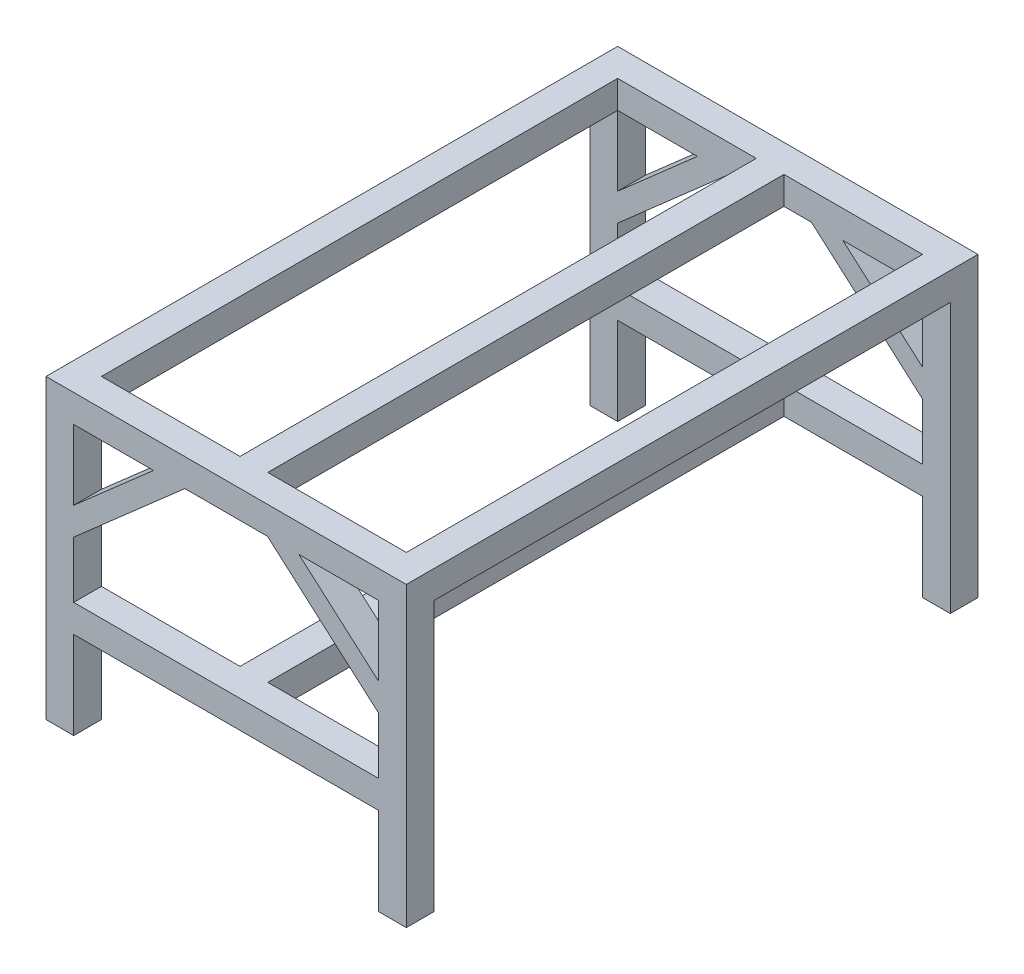
SolidWorks part; units mm, degrees
ref_plane "Front Plane" through (0, 0, 0) normal (0, 0, 1) x (1, 0, 0)
ref_plane "Top Plane" through (0, 0, 0) normal (0, 1, 0) x (1, 0, 0)
ref_plane "Right Plane" through (0, 0, 0) normal (1, 0, 0) x (0, 0, -1)
sketch "Sketch1" plane through (0, 0, 0) normal (0, 0, 1) x (1, 0, 0)
  line L0 (0, 0) -> (1040, 0)
  line L1 (639.2329, -80) -> (960, -361.6709)
  line L2 (960, -282.0611) -> (729.8927, -80)
  line L3 (960, -857.8) -> (960, -80)
  line L4 (960, -80) -> (80, -80)
  line L5 (80, -524.8) -> (960, -524.8)
  line L6 (0, 0) -> (0, -857.8)
  line L7 (0, -857.8) -> (80, -857.8)
  line L8 (80, -857.8) -> (80, -80)
  line L9 (80, -282.0611) -> (310.1073, -80)
  line L10 (400.7671, -80) -> (80, -361.6709)
  line L11 (520, -88.6285) -> (520, 45.2734) construction
  line L12 (1040, -857.8) -> (960, -857.8)
  line L13 (1040, 0) -> (1040, -857.8)
  line L14 (80, -604.8) -> (960, -604.8)
  line L19 (1683.668, -404.8) -> (-735.428, -404.8) construction
  point P16 (520, 0)
  point P23 (520, -80)
  dimension "D1" = 857.8
  dimension "D2" = 1040
  dimension "D3" = 80
  dimension "D4" = 80
  dimension "D5" = 80
  dimension "D6" = 200
extrude "Boss-Extrude1" add sketch "Sketch1" against normal blind 80 contours L4 L11 L0 L6 L7 L8 | L10 L4 L9 L8 | L2 L4 L1 L3 | L11 L4 L3 L12 L13 L0 | L8 L14 L3 L5
sketch "Sketch2" plane through (0, 0, -80) normal (0, 0, -1) x (-1, 0, 0)
  line L1 (-1040, 0) -> (-960, 0)
  line L2 (-1040, 0) -> (-1040, -80)
  line L3 (-1040, -80) -> (-960, -80)
  line L4 (-960, 0) -> (-960, -80)
  line L5 (-80, -80) -> (0, -80)
  line L6 (-80, -80) -> (-80, 0)
  line L7 (-80, 0) -> (0, 0)
  line L8 (0, -80) -> (0, 0)
  line L9 (-560, -524.8) -> (-480, -524.8)
  line L10 (-560, -524.8) -> (-560, -604.8)
  line L11 (-560, -604.8) -> (-480, -604.8)
  line L12 (-480, -524.8) -> (-480, -604.8)
  line L13 (-80, -604.8) -> (-960, -604.8) construction
  line L14 (-80, -524.8) -> (-960, -524.8) construction
  line L15 (-960, -524.8) -> (-960, -361.6709) construction
  line L17 (-639.2329, -80) -> (-400.7671, -80) construction
  line L18 (-480, -80) -> (-560, -80)
  line L19 (-480, -80) -> (-480, 0)
  line L20 (-480, 0) -> (-560, 0)
  line L21 (-560, -80) -> (-560, 0)
  line L22 (0, 0) -> (-1040, 0) construction
  dimension "D1" = 80
  dimension "D2" = 400
extrude "Boss-Extrude2" add sketch "Sketch2" along normal blind 790
ref_plane "Plane2" through (0, 0, -825) normal (0, 0, 1) x (1, 0, 0)
mirror "Mirror2" about plane through (0, 0, -825) normal (0, 0, 1) of "Boss-Extrude2"
mirror "Mirror3" about plane through (0, 0, -825) normal (0, 0, 1) of "Boss-Extrude1"
